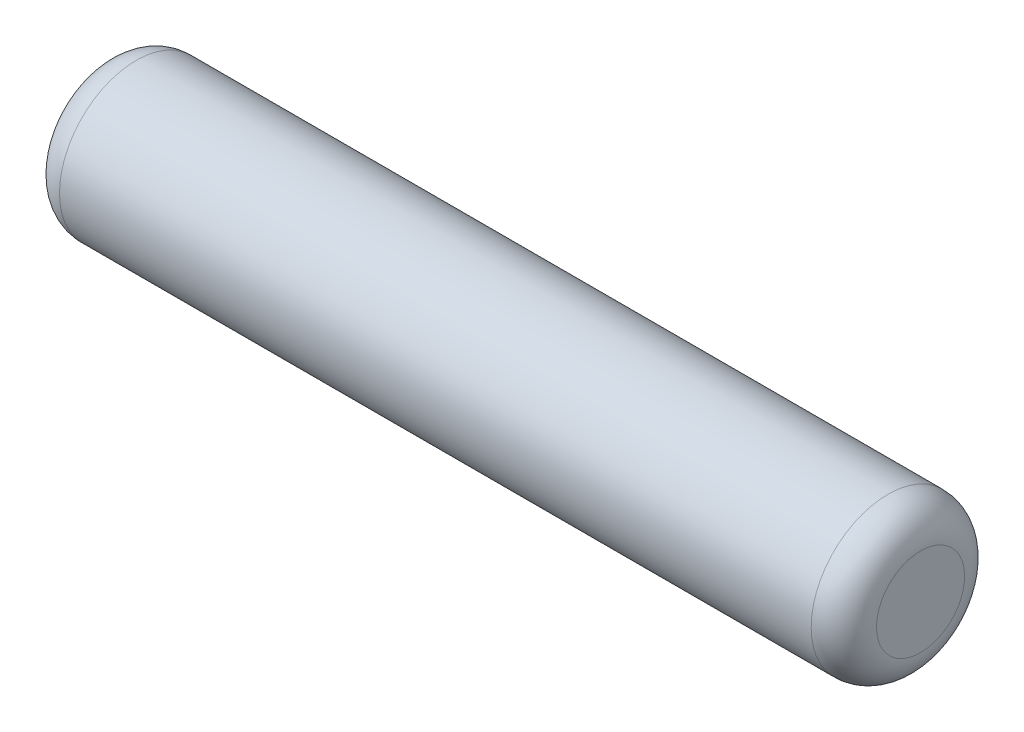
SolidWorks part; units mm, degrees
ref_plane "Plane1" through (0, 0, 0) normal (0, 0, 1) x (1, 0, 0)
ref_plane "Plane2" through (0, 0, 0) normal (0, 1, 0) x (1, 0, 0)
ref_plane "Plane3" through (0, 0, 0) normal (1, 0, 0) x (0, 0, -1)
sketch "Sketch1" plane through (0, 0, 0) normal (0, 0, 1) x (1, 0, 0)
  line L1 (-6.35, 0) -> (47.0909, 0) construction
  line L2 (0, 0) -> (12.7, 0)
  line L3 (12.7, 0) -> (12.7, 0.6845)
  line L5 (12.192, 1.1925) -> (0.508, 1.1925)
  line L6 (0, 0.6845) -> (0, 0)
  arc A0 (0.508, 1.1925) -> (0, 0.6845) centre (0.508, 0.6845) ccw
  arc A1 (12.7, 0.6845) -> (12.192, 1.1925) centre (12.192, 0.6845) ccw
  point P8 (0, 1.1925)
  point P11 (12.7, 1.1925)
  dimension "D1" = 0.508
  dimension "Diameter" = 2.3851
  dimension "Length" = 12.7
revolve "Base-Revolve" add sketch "Sketch1" angle 360 about L1
